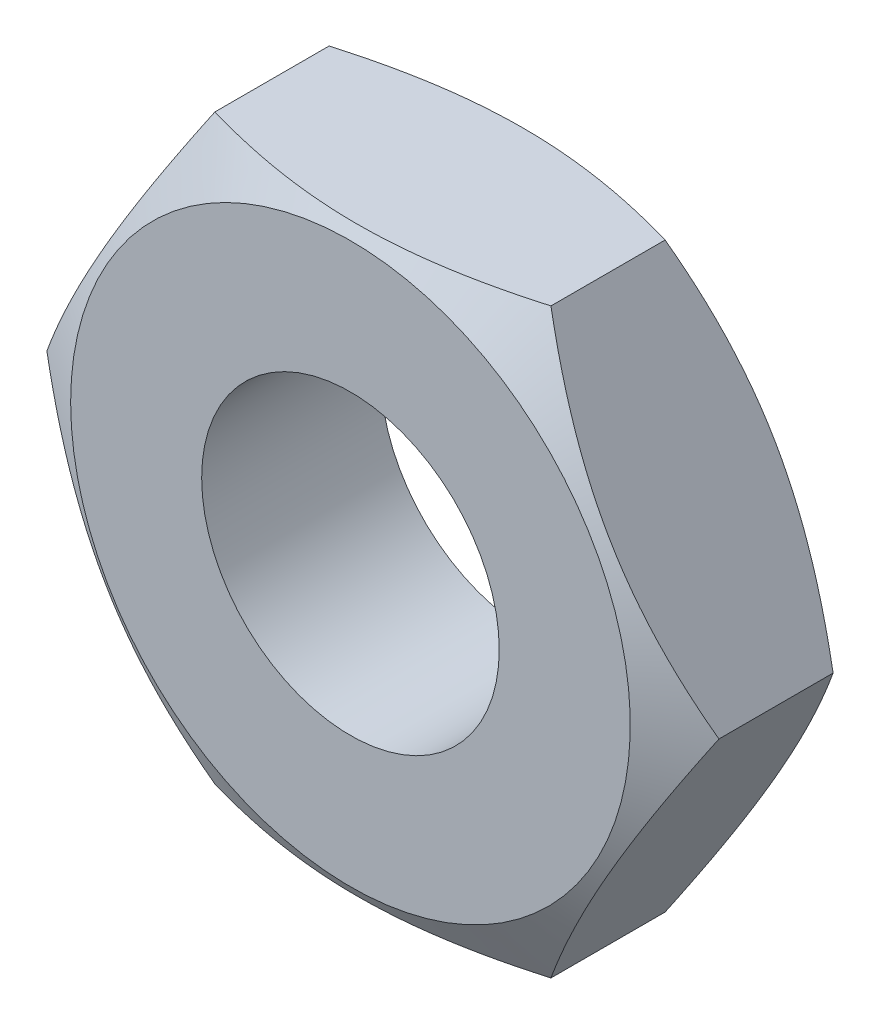
SolidWorks part; units mm, degrees
extrude "Base-Extrusion" add sketch "Esquisse1" along normal blind 4
sketch "Esquisse1" plane through (0, 0, 0) normal (0, 0, 1) x (1, 0, 0)
  line L0 (0, 0) -> (0, 60.5083) construction
  line L1 (0, 0) -> (52.6683, 0) construction
  line L2 (-7.5056, 0) -> (-3.7528, 6.5)
  line L3 (-3.7528, 6.5) -> (3.7528, 6.5)
  line L4 (3.7528, 6.5) -> (7.5056, 0)
  line L5 (7.5056, 0) -> (3.7528, -6.5)
  line L6 (3.7528, -6.5) -> (-3.7528, -6.5)
  line L7 (-3.7528, -6.5) -> (-7.5056, 0)
  dimension "D1" = 120
  dimension "D2" = 13
extrude "Enlèv. mat.-Extru.1" cut sketch "Esquisse2" against normal through all
sketch "Esquisse2" plane through (0, 0, 4) normal (0, 0, 1) x (1, 0, 0)
  circle A0 centre (0, 0) radius 3.3234
  dimension "D1" = 6.6469
cosmetic thread "Représentation de filetage1" parameters "D2"=8
ref_plane "Plane1" through (0, 0, 0) normal (0, 0, 1) x (1, 0, 0)
ref_plane "Plane2" through (0, 0, 0) normal (0, 1, 0) x (1, 0, 0)
ref_plane "Plane3" through (0, 0, 0) normal (1, 0, 0) x (0, 0, -1)
sketch "Esquisse3" plane through (0, 0, 0) normal (0, 1, 0) x (1, 0, 0)
  line L0 (0, 0) -> (0, -2.6293) construction
  line L1 (0, 0) -> (0, -4) construction
  line L2 (-3.7528, 0) -> (3.7528, 0) construction
  line L3 (-7.5056, -4) -> (-7.5056, 0) construction
  line L4 (-7.5056, 0) -> (-3.7528, 0) construction
  line L5 (-6.25, 0) -> (-7.5056, 0)
  line L6 (-6.25, 0) -> (-7.5056, -0.7249)
  line L8 (-7.5056, 0) -> (-7.5056, -0.7249)
  dimension "D2" = 6.25
  dimension "D1" = 30
revolve "Enlever de la matière-Révolution1" cut sketch "Esquisse3" angle 360 about L0
ref_plane "Plan4" through (0, 0, 2) normal (0, 0, -1) x (-1, 0, 0)
mirror "Symétrie1"
equation "\"D2@Esquisse3\" =( \"D2@Esquisse1\"-0.5)/2"
equation "\"D1@Plan4\" = \"D1@Base-Extrusion\"/2"
